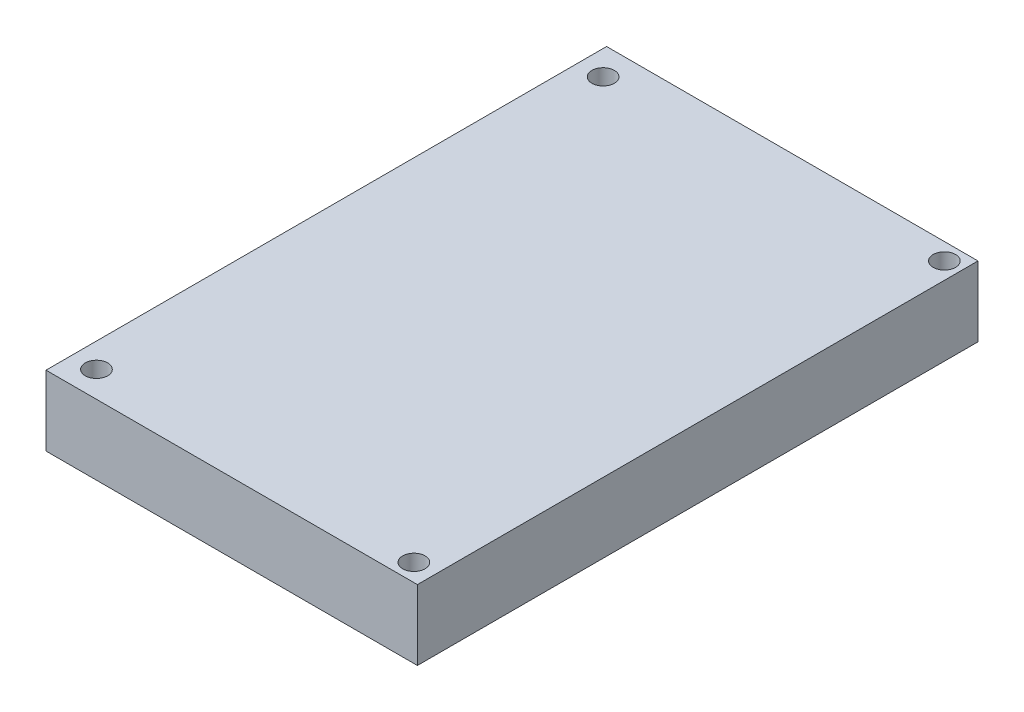
SolidWorks part; units mm, degrees
ref_plane "Front Plane" through (0, 0, 0) normal (0, 0, 1) x (1, 0, 0)
ref_plane "Top Plane" through (0, 0, 0) normal (0, 1, 0) x (1, 0, 0)
ref_plane "Right Plane" through (0, 0, 0) normal (1, 0, 0) x (0, 0, -1)
sketch "Sketch1" plane through (0, 0, 0) normal (0, 1, 0) x (1, 0, 0)
  line L1 (-26.5, -40) -> (26.5, -40)
  line L2 (-26.5, -40) -> (-26.5, 40)
  line L3 (-26.5, 40) -> (26.5, 40)
  line L4 (26.5, -40) -> (26.5, 40)
  line L5 (-26.5, -40) -> (26.5, 40) construction
  line L6 (-26.5, 40) -> (26.5, -40) construction
  circle A0 centre (-23, 36) radius 1.6
  circle A1 centre (24.1, 37.6) radius 1.6
  circle A2 centre (23.5, -37.5) radius 1.6
  circle A3 centre (-23, -36.3) radius 1.6
  point P0 (0, 0)
  dimension "D3" = 3.2
  dimension "D5" = 3.5
  dimension "D7" = 2.4
  dimension "D8" = 2.5
  dimension "D10" = 3.7
  dimension "D11" = 3.5
  dimension "D1" = 53
  dimension "D2" = 80
  dimension "D4" = 4
  dimension "D6" = 2.4
  dimension "D9" = 3
extrude "Boss-Extrude1" add sketch "Sketch1" along normal blind 10
